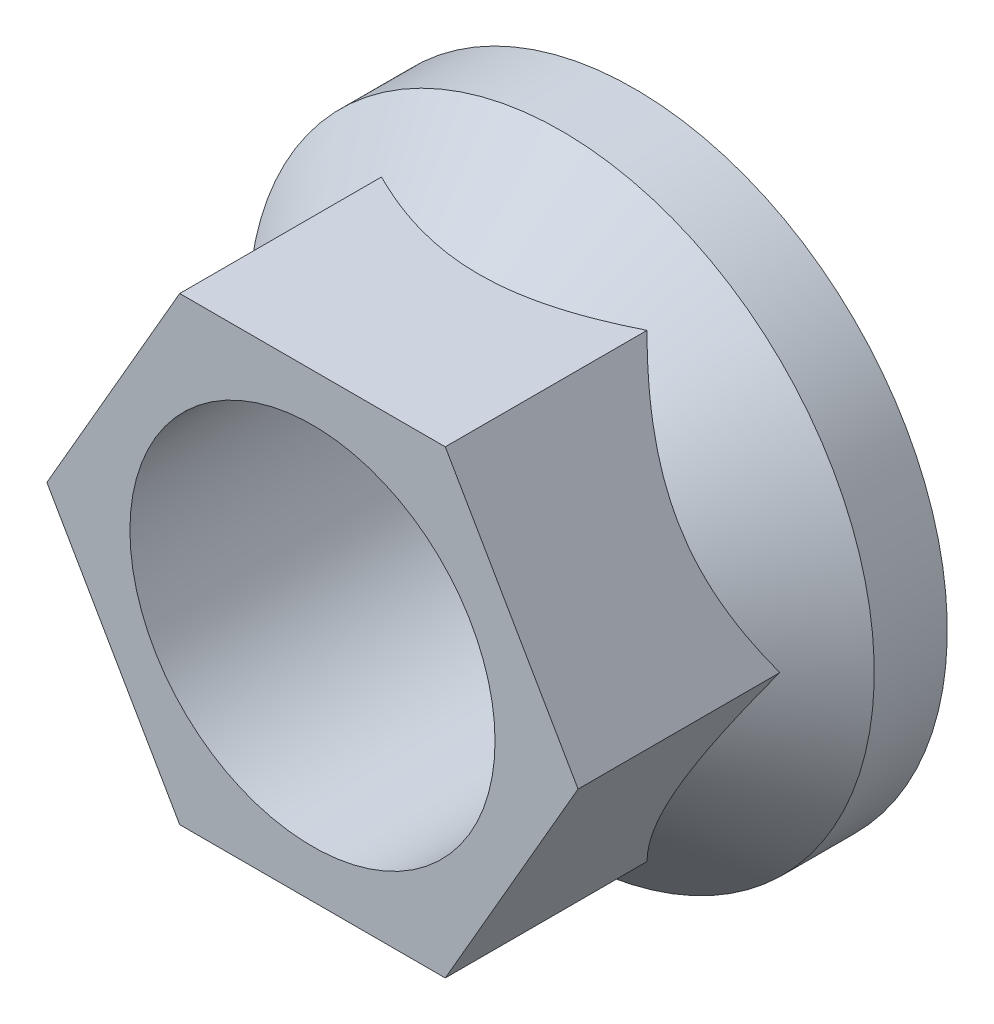
SolidWorks part; units mm, degrees
material "Alloy Steel"
ref_plane "X-Y Datum" through (0, 0, 0) normal (0, 0, 1) x (1, 0, 0)
ref_plane "X-Z Datum" through (0, 0, 0) normal (0, 1, 0) x (1, 0, 0)
ref_plane "Y-Z Datum" through (0, 0, 0) normal (1, 0, 0) x (0, 0, -1)
sketch "Sketch1" plane through (0, 0, 0) normal (1, 0, 0) x (0, 0, -1)
  line L4 (0, 3.9688) -> (-7, 3.9687)
  line L5 (0, 0) -> (-39678.0303, 0) construction
  line L7 (-7, 3.9687) -> (-7, 4.7625)
  line L8 (-7, 4.7625) -> (-3.625, 4.7625)
  line L9 (-3.625, 4.7625) -> (-1.5875, 6.8)
  line L10 (-1.5875, 6.8) -> (0, 6.8)
  line L11 (0, 6.8) -> (0, 3.9688)
  dimension "D1" = 7.9375
  dimension "D2" = 9.525
  dimension "D3" = 7
  dimension "D4" = 13.6
  dimension "D5" = 1.5875
  dimension "D6" = 45
revolve "Revolve1" add sketch "Sketch1" angle 360 about L5
sketch "Sketch2" plane through (0, 0, 7) normal (0, 0, 1) x (1, 0, 0)
  line L1 (-2.8868, 5) -> (-5.7735, 0)
  line L2 (-5.7735, 0) -> (-2.8868, -5)
  line L3 (-2.8868, -5) -> (2.8868, -5)
  line L4 (2.8868, -5) -> (5.7735, 0)
  line L5 (5.7735, 0) -> (2.8868, 5)
  line L6 (2.8868, 5) -> (-2.8868, 5)
  circle A0 centre (0, 0) radius 5 construction
  circle A1 centre (0, 0) radius 3.9687 construction
  circle A2 centre (0, 0) radius 3.9687
  dimension "D1" = 10
extrude "Boss-Extrude1" add sketch "Sketch2" against normal up to surface (4.386 mm away)
move or copy body "Body-Move/Copy1" [suppressed] bodies to move or copy 102
